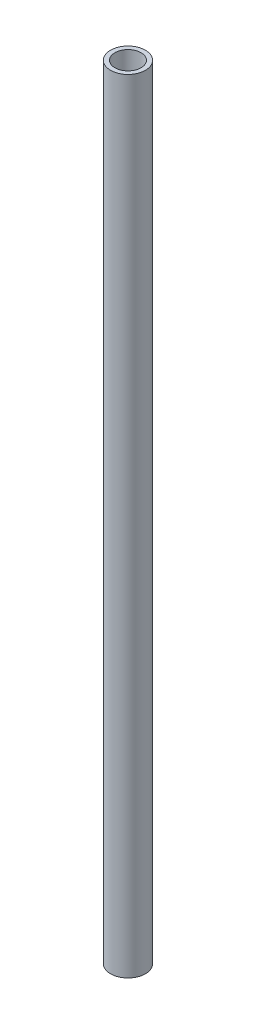
SolidWorks part; units mm, degrees
material "Thornel Mat VMA"
ref_plane "Front Plane" through (0, 0, 0) normal (0, 0, 1) x (1, 0, 0)
ref_plane "Top Plane" through (0, 0, 0) normal (0, 1, 0) x (1, 0, 0)
ref_plane "Right Plane" through (0, 0, 0) normal (1, 0, 0) x (0, 0, -1)
sketch "Sketch1" plane through (0, 0, 0) normal (0, 1, 0) x (1, 0, 0)
  circle A0 centre (0, 0) radius 6.35
  dimension "D1" = 12.7
extrude "Boss-Extrude1" add sketch "Sketch1" along normal blind 285
sketch "Sketch2" plane through (0, 0, 0) normal (0, -1, 0) x (1, 0, 0)
  circle A0 centre (0, 0) radius 4.765
  dimension "D1" = 9.53
extrude "Cut-Extrude1" cut sketch "Sketch2" against normal up to next
